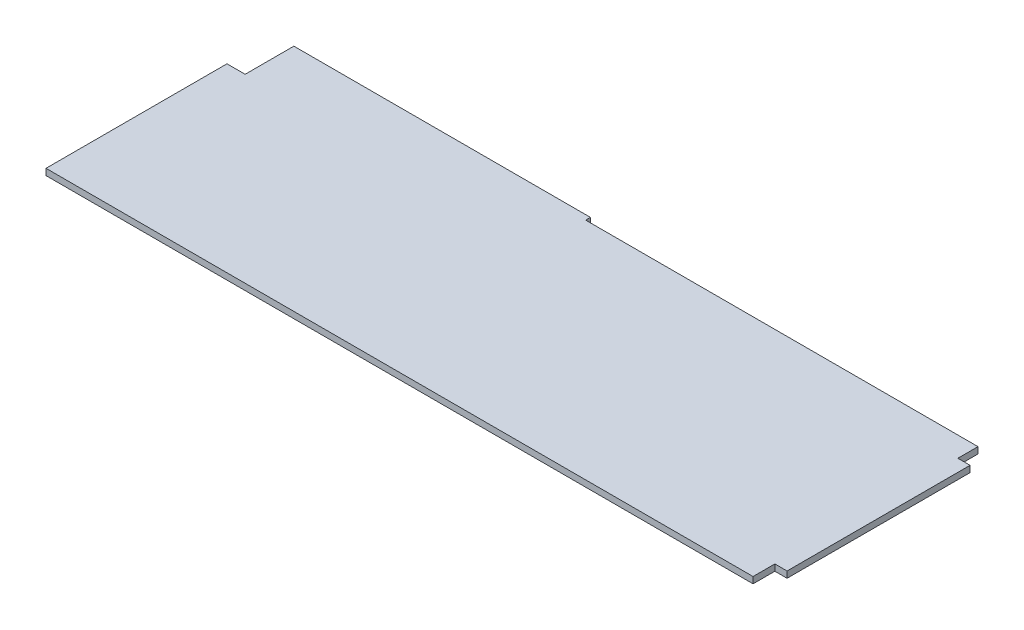
SolidWorks part; units mm, degrees
ref_plane "Front Plane" through (0, 0, 0) normal (0, 0, 1) x (1, 0, 0)
ref_plane "Top Plane" through (0, 0, 0) normal (0, 1, 0) x (1, 0, 0)
ref_plane "Right Plane" through (0, 0, 0) normal (1, 0, 0) x (0, 0, -1)
sketch "Sketch1" plane through (0, 0, 0) normal (0, 1, 0) x (1, 0, 0)
  line L0 (0, 0) -> (0, 75.95)
  line L1 (0, 75.95) -> (7.62, 75.95)
  line L2 (7.62, 75.95) -> (7.62, 96.4)
  line L3 (7.62, 96.4) -> (132.07, 96.4)
  line L4 (132.07, 96.4) -> (132.07, 94.4)
  line L5 (132.07, 94.4) -> (296.72, 94.4)
  line L6 (296.72, 0) -> (296.72, 9.15)
  line L7 (296.72, 9.15) -> (301.84, 9.15)
  line L8 (301.84, 9.15) -> (301.84, 85.95)
  line L9 (301.84, 85.95) -> (296.72, 85.95)
  line L10 (296.72, 85.95) -> (296.72, 94.4)
  line L11 (296.72, 85.95) -> (296.72, 9.15) construction
  line L13 (296.72, 0) -> (0, 0)
  dimension "D1" = 2
  dimension "D2" = 301.84
  dimension "D3" = 5.12
  dimension "D4" = 9.15
  dimension "D5" = 8.45
  dimension "D8" = 75.95
  dimension "D9" = 7.62
  dimension "D10" = 132.07
  dimension "D11" = 96.4
extrude "Boss-Extrude1" add sketch "Sketch1" along normal blind 2.67
